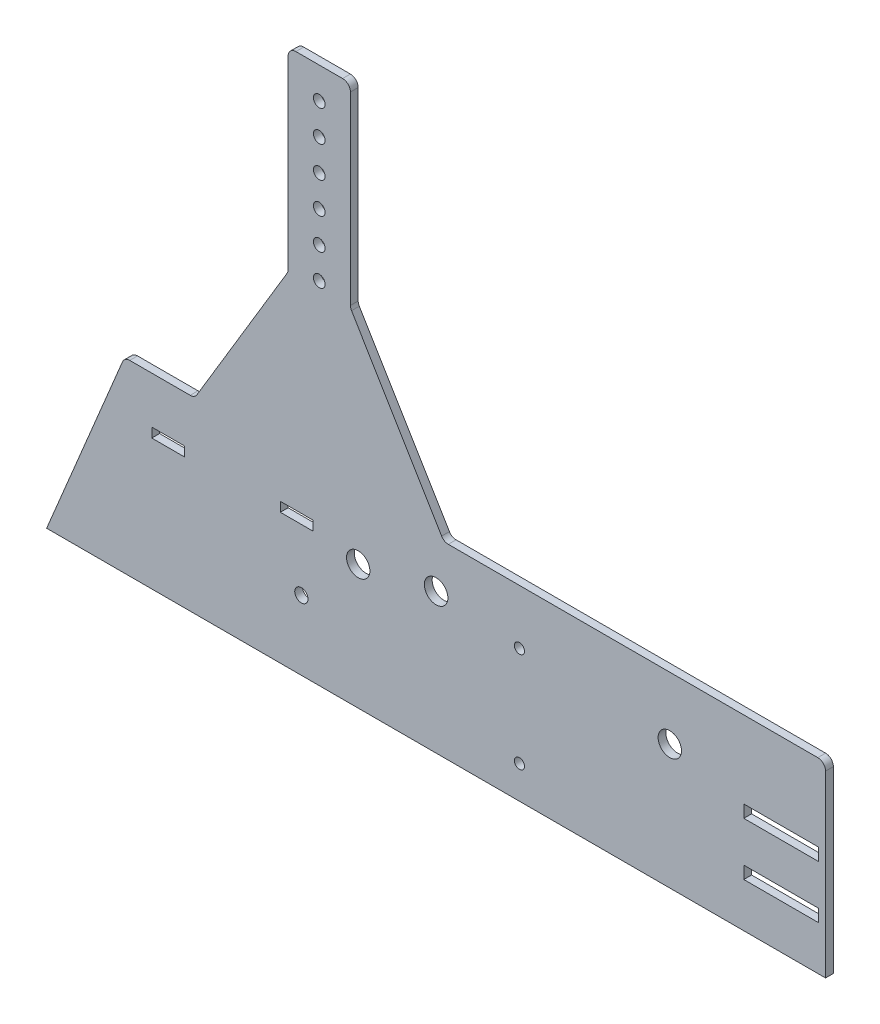
SolidWorks part; units mm, degrees
material "1.0038 (S235JRG2)"
ref_plane "Plan de face" through (0, 0, 0) normal (0, 0, 1) x (1, 0, 0)
ref_plane "Plan de dessus" through (0, 0, 0) normal (0, 1, 0) x (1, 0, 0)
ref_plane "Plan de droite" through (0, 0, 0) normal (1, 0, 0) x (0, 0, -1)
sketch "Esquisse1" plane through (0, 0, 0) normal (0, 0, 1) x (1, 0, 0)
  line L0 (0, 0) -> (-1000, 0)
  line L1 (-1000, 0) -> (-900, 240)
  line L2 (-900, 240) -> (-810, 240)
  line L3 (0, 240) -> (0, 0)
  line L4 (-810, 240) -> (-690, 440)
  line L5 (-690, 440) -> (-690, 690)
  line L6 (-690, 690) -> (-610, 690)
  line L7 (-600, 160) -> (-494.1499, 457.1231) construction
  line L8 (-490, 240) -> (0, 240)
  line L9 (-105, 141) -> (-9, 141)
  line L10 (-105, 141) -> (-105, 125)
  line L11 (-105, 125) -> (-9, 125)
  line L12 (-9, 141) -> (-9, 125)
  line L13 (-105, 73) -> (-9, 73)
  line L14 (-105, 73) -> (-105, 57)
  line L15 (-105, 57) -> (-9, 57)
  line L16 (-9, 73) -> (-9, 57)
  line L29 (-610, 690) -> (-610, 440)
  line L30 (-610, 440) -> (-490, 240)
  line L32 (-865, 167.8) -> (-823, 167.8)
  line L33 (-865, 167.8) -> (-865, 180)
  line L34 (-865, 180) -> (-823, 180)
  line L35 (-823, 167.8) -> (-823, 180)
  line L36 (-700, 167.8) -> (-658, 167.8)
  line L37 (-700, 167.8) -> (-700, 180)
  line L38 (-700, 180) -> (-658, 180)
  line L39 (-658, 167.8) -> (-658, 180)
  circle A0 centre (-200, 160) radius 15
  circle A1 centre (-600, 160) radius 15
  circle A2 centre (-393, 170) radius 6.5
  circle A3 centre (-393, 42) radius 6.5
  circle A4 centre (-673, 89) radius 8.5
  circle A5 centre (-500, 180) radius 15.1
  circle A11 centre (-650, 650) radius 7.5
  circle A12 centre (-650, 610) radius 7.5
  circle A13 centre (-650, 570) radius 7.5
  circle A14 centre (-650, 530) radius 7.5
  circle A15 centre (-650, 490) radius 7.5
  circle A16 centre (-650, 450) radius 7.5
  point P27 (0, 0)
  point P30 (-543, 320)
  point P57 (-650, 690)
extrude "Boss.-Extru.1" add sketch "Esquisse1" along normal blind 10
fillet "Congé1" radius 10 8 edges at (0, 240, 5) (-490, 240, 5) (-610, 440, 5) (-610, 690, 5) (-690, 690, 5) (-690, 440, 5) (-810, 240, 5) (-900, 240, 5)
equation "\"D20@Esquisse1\"=\"D19@Esquisse1\""
